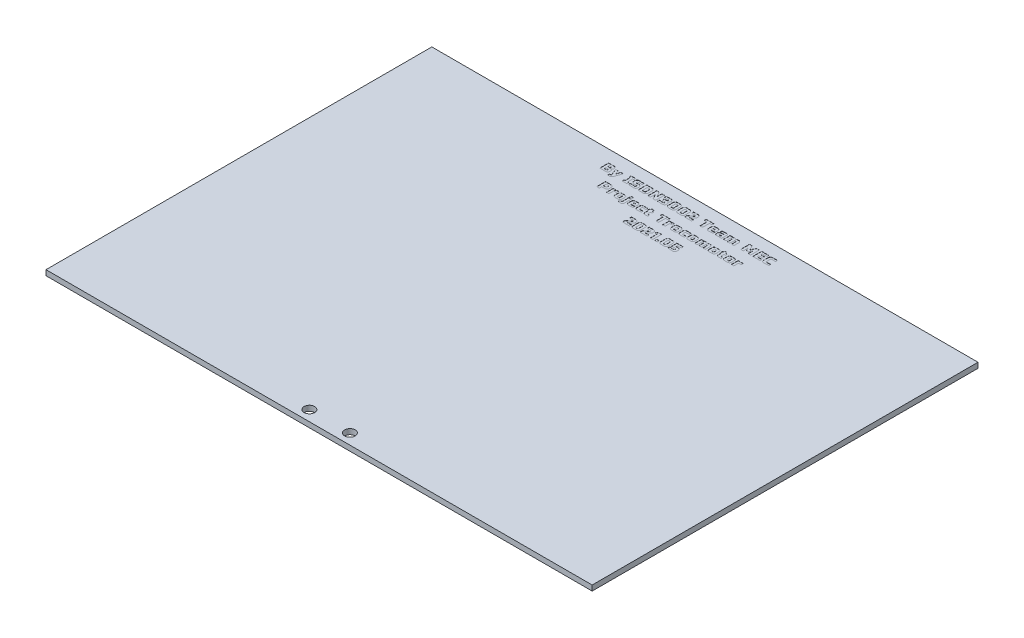
SolidWorks part; units mm, degrees
ref_plane "前视基准面" through (0, 0, 0) normal (0, 0, 1) x (1, 0, 0)
ref_plane "上视基准面" through (0, 0, 0) normal (0, 1, 0) x (1, 0, 0)
ref_plane "右视基准面" through (0, 0, 0) normal (1, 0, 0) x (0, 0, -1)
sketch "Sketch1" plane through (0, 0, 0) normal (0, 1, 0) x (1, 0, 0)
  line L0 (-155, -103.5) -> (155, -103.5) construction
  line L1 (-155, 109.5) -> (155, 109.5)
  line L2 (-155, 109.5) -> (-155, -109.5)
  line L3 (-155, -109.5) -> (155, -109.5)
  line L4 (155, 109.5) -> (155, -109.5)
  line L5 (-155, 109.5) -> (155, -109.5) construction
  line L6 (-155, -109.5) -> (155, 109.5) construction
  line L7 (-11.5, -103.5) -> (11.5, -103.5) construction
  circle A0 centre (-11.5, -103.5) radius 3
  circle A1 centre (11.5, -103.5) radius 3
  point P0 (0, 0)
  point P11 (0, -103.5)
  dimension "D4" = 6
  dimension "D5" = 6
  dimension "D1" = 213
  dimension "D2" = 310
  dimension "D3" = 23
  dimension "D6" = 6
extrude "Boss-Extrude1" add sketch "Sketch1" along normal blind 3
sketch "Sketch2" plane through (0, 3, 0) normal (0, 1, 0) x (1, 0, 0)
  line L0 (-155, 97.6296) -> (155, 97.6296) construction
  line L1 (-155, 109.5) -> (-155, -109.5) construction
  line L2 (155, -109.5) -> (155, 109.5) construction
  text T0 "By ISDN3002 Team MEC\r\nProject Trocomotor\r\n2021.05" font "Russo One" height 5
extrude "Cut-Extrude1" cut sketch "Sketch2" against normal blind 0.1
